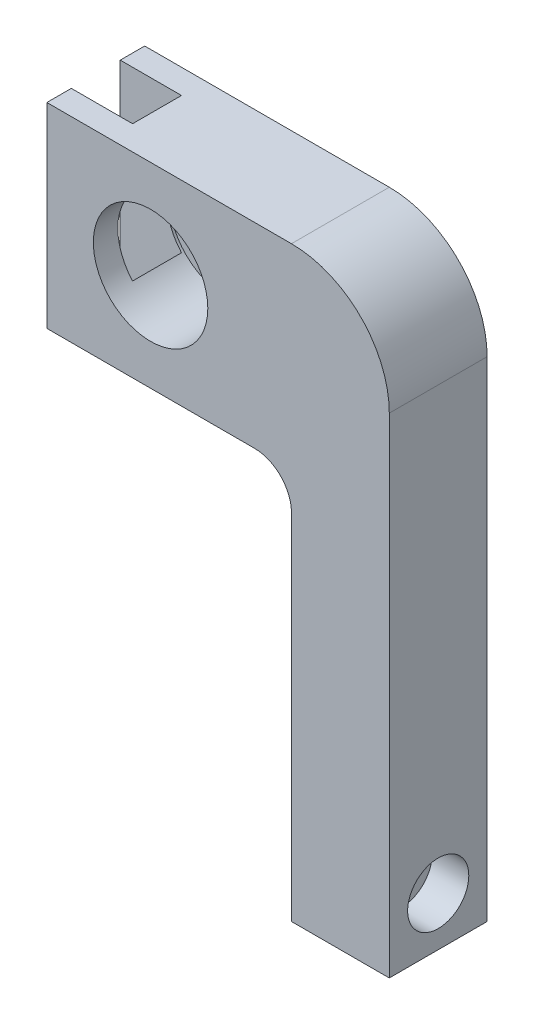
SolidWorks part; units mm, degrees
ref_plane "Front Plane" through (0, 0, 0) normal (0, 0, 1) x (1, 0, 0)
ref_plane "Top Plane" through (0, 0, 0) normal (0, 1, 0) x (1, 0, 0)
ref_plane "Right Plane" through (0, 0, 0) normal (1, 0, 0) x (0, 0, -1)
sketch "Sketch1" plane through (0, 0, 0) normal (0, 0, 1) x (1, 0, 0)
  line L0 (0, 0) -> (0, 127)
  line L1 (-25.4, 152.4) -> (-88.9, 152.4)
  line L2 (-88.9, 152.4) -> (-88.9, 101.6)
  line L3 (-88.9, 101.6) -> (-35.052, 101.6)
  line L4 (-25.4, 91.948) -> (-25.4, 0)
  line L5 (-25.4, 0) -> (0, 0)
  arc A0 (-35.052, 101.6) -> (-25.4, 91.948) centre (-35.052, 91.948) cw
  arc A1 (-25.4, 152.4) -> (0, 127) centre (-25.4, 127) cw
  dimension "D1" = 9.652
  dimension "D2" = 25.4
  dimension "D3" = 25.4
  dimension "D4" = 152.4
  dimension "D5" = 50.8
  dimension "D6" = 88.9
extrude "Boss-Extrude1" add sketch "Sketch1" along normal mid plane 25.4
sketch "Sketch2" plane through (0, 152.4, 0) normal (0, 1, 0) x (1, 0, 0)
  line L0 (-88.9, -12.7) -> (-88.9, 12.7) construction
  line L1 (-72.9996, 6.35) -> (-88.9, 6.35)
  line L2 (-72.9996, 6.35) -> (-72.9996, -6.35)
  line L3 (-72.9996, -6.35) -> (-88.9, -6.35)
  line L4 (-88.9, 6.35) -> (-88.9, -6.35)
  line L5 (-72.9996, 6.35) -> (-88.9, -6.35) construction
  line L6 (-72.9996, -6.35) -> (-88.9, 6.35) construction
  point P0 (-80.9498, 0)
  dimension "D1" = 12.7
  dimension "D2" = 15.9004
extrude "Cut-Extrude1" cut sketch "Sketch2" against normal through all both and the other way through all
hole_wizard "CBORE for #00 Binding Head Machine Screw1" positions "Sketch4" profile "Sketch5" counterbore size "#00" standard "ANSI Inch" end condition through all
sketch "Sketch4" plane through (0, 0, 12.7) normal (0, 0, 1) x (1, 0, 0)
  line L0 (-88.9, 152.4) -> (-88.9, 101.6) construction
  line L1 (-25.4, 152.4) -> (-88.9, 152.4) construction
  point P0 (-61.976, 127)
  dimension "D1" = 26.924
  dimension "D2" = 25.4
sketch "Sketch5" plane through (-61.976, 127, 12.7) normal (1, 0, 0) x (0, -1, 0)
  line L0 (0, 0) -> (0, 25.4)
  line L1 (0, 25.4) -> (6.35, 25.4)
  line L3 (6.35, 25.4) -> (6.35, 19.7104)
  line L4 (6.35, 19.7104) -> (14.859, 19.7104)
  line L5 (14.859, 19.7104) -> (14.859, 0)
  line L7 (14.859, 0) -> (0, 0)
  line L11 (0, -6.35) -> (0, 107.95) construction
  dimension "Thru Hole Dia." = 12.7
  dimension "Thru Hole Depth" = 25.4
  dimension "C'Bore Dia." = 29.718
  dimension "C'Bore Depth" = 19.7104
hole_wizard "CBORE for 3/8 Socket Head Cap Screw1" positions "Sketch6" profile "Sketch7" counterbore size "3/8" standard "ANSI Inch" end condition through all
sketch "Sketch6" plane through (0, 0, 0) normal (1, 0, 0) x (0, 0, -1)
  line L0 (-12.7, 0) -> (12.7, 0) construction
  point P0 (0, 12.7)
  dimension "D1" = 12.7
sketch "Sketch7" plane through (0, 12.7, 0) normal (0, 1, 0) x (0, 0, -1)
  line L0 (0, 0) -> (0, 88.9)
  line L1 (0, 88.9) -> (5.0419, 88.9)
  line L2 (5.0419, 9.7005) -> (5.0419, 88.9)
  line L3 (5.0419, 9.7005) -> (5.334, 9.525)
  line L4 (5.334, 9.525) -> (7.9375, 9.525)
  line L5 (7.9375, 9.525) -> (7.9375, 0)
  line L7 (0, 0) -> (7.9375, 0)
  line L9 (-5.0419, 9.7005) -> (-5.334, 9.525) construction
  line L11 (0, -6.35) -> (0, 107.95) construction
  dimension "Thru Hole Dia." = 10.0838
  dimension "Thru Hole Depth" = 88.9
  dimension "C'Bore Dia." = 15.875
  dimension "C'Bore Depth" = 9.525
  dimension "Mid C'Sink Dia." = 10.668
  dimension "Mid C'Sink Angle" = 118
hole_wizard "#8-32 Tapped Hole1" positions "Sketch8" profile "Sketch9" tap size "#8-32" standard "ANSI Inch"
sketch "Sketch8" plane through (-88.9, 0, 0) normal (-1, 0, 0) x (0, 0, 1)
  line L0 (-12.7, 152.4) -> (-12.7, 101.6) construction
  line L1 (-6.35, 101.6) -> (-12.7, 101.6) construction
  point P0 (-9.525, 104.775)
  dimension "D1" = 3.175
  dimension "D2" = 3.175
sketch "Sketch9" plane through (-88.9, 104.775, -9.525) normal (0, 1, 0) x (0, 0, 1)
  line L0 (0, 0) -> (0, 9.9278)
  line L1 (0, 9.9278) -> (1.7272, 8.89)
  line L2 (1.7272, 8.89) -> (1.7272, 0)
  line L5 (1.7272, 0) -> (0, 0)
  line L10 (0, 9.9278) -> (-1.7272, 8.89) construction
  line L11 (0, -6.35) -> (0, 107.95) construction
  dimension "Tap Drill Dia." = 3.4544
  dimension "Tap Drill Depth" = 8.89
  dimension "Drill Angle" = 118
cosmetic thread "Hole Thread1" parameters "D1"=8.3312, "D2"=4.1656
pattern_linear "LPattern1" count 2 spacing 44.45 along (0, 1, 0) count 2 spacing 19.05 along (0, 0, 1) of "#8-32 Tapped Hole1"
